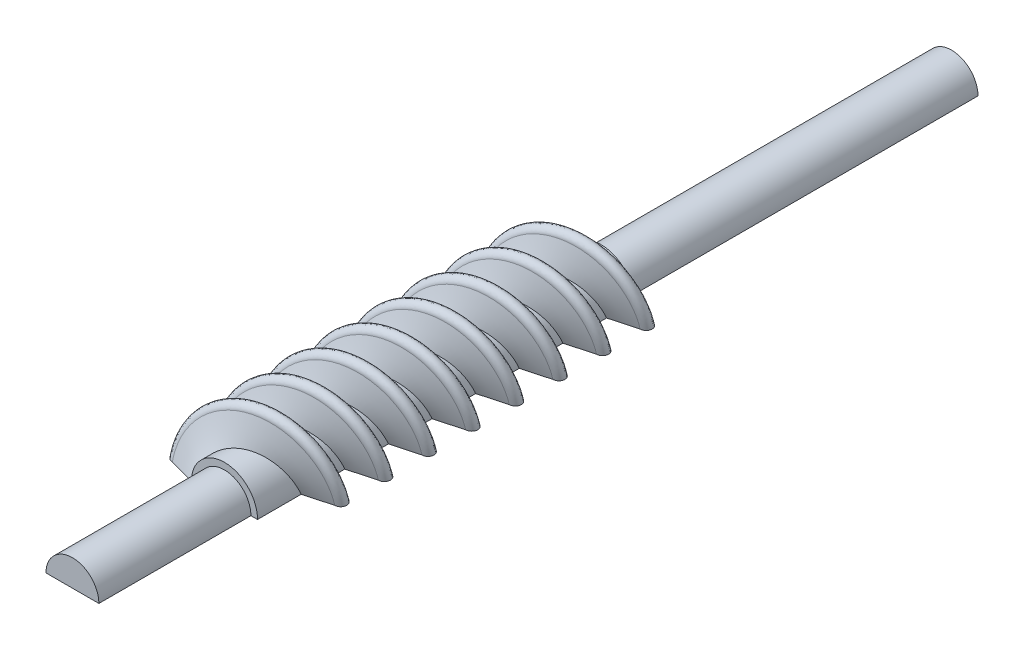
SolidWorks part; units mm, degrees
ref_plane "Plan de face" through (0, 0, 0) normal (0, 0, 1) x (1, 0, 0)
ref_plane "Plan de dessus" through (0, 0, 0) normal (0, 1, 0) x (1, 0, 0)
ref_plane "Plan de droite" through (0, 0, 0) normal (1, 0, 0) x (0, 0, -1)
sketch "Esquisse1" plane through (0, 0, 0) normal (0, 0, 1) x (1, 0, 0)
  circle A0 centre (0, 0) radius 5
  dimension "D1" = 10
extrude "Boss.-Extru.1" add sketch "Esquisse1" along normal blind 55
sketch "Esquisse3" plane through (0, 0, 55) normal (0, 0, 1) x (1, 0, 0)
  circle A0 centre (0, 0) radius 5
curve "Hélice/Spirale1" pitch 13.2 height 52.8 turns 4
sketch "Esquisse4" plane through (0, 0, 0) normal (0, 1, 0) x (1, 0, 0)
  line L0 (-5, -55) -> (-9, -55) construction
  line L1 (-5, 0) -> (-5, -55) construction
  line L2 (-9, -54.1) -> (-5, -53)
  line L3 (-9, -55.9) -> (-5, -57)
  line L5 (-5, -53) -> (-4.702, -53)
  line L6 (-4.702, -53) -> (-4.702, -57)
  line L7 (-4.702, -57) -> (-5, -57)
  arc A1 (-9, -54.1) -> (-9, -55.9) centre (-9, -55) ccw
  spline S0 degree 3 poles (-5, -55) (-5, -54.7265) (-4.7397, -54.1743) (-3.6276, -53.3502) (-1.9632, -52.525) (0, -51.7) (1.9632, -50.875) (3.6276, -50.05) (4.7397, -49.225) (5.1302, -48.4) (4.7397, -47.575) (3.6276, -46.75) (1.4084, -45.65) (-1.4084, -44.55) (-3.6276, -43.45) (-4.7397, -42.625) (-5.1302, -41.8) (-4.7397, -40.975) (-3.6276, -40.15) (-1.4084, -39.05) (1.4084, -37.95) (3.6276, -36.85) (4.7397, -36.025) (5.1302, -35.2) (4.7397, -34.375) (3.6276, -33.55) (1.4084, -32.45) (-1.4084, -31.35) (-3.6276, -30.25) (-4.7397, -29.425) (-5.1302, -28.6) (-4.7397, -27.775) (-3.6276, -26.95) (-1.4084, -25.85) (1.4084, -24.75) (3.6276, -23.65) (4.7397, -22.825) (5.1302, -22) (4.7397, -21.175) (3.6276, -20.35) (1.4084, -19.25) (-1.4084, -18.15) (-3.6276, -17.05) (-4.7397, -16.225) (-5.1302, -15.4) (-4.7397, -14.575) (-3.6276, -13.75) (-1.4084, -12.65) (1.4084, -11.55) (3.6276, -10.45) (4.7397, -9.625) (5.1302, -8.8) (4.7397, -7.975) (3.6276, -7.15) (1.9632, -6.325) (0, -5.5) (-1.9632, -4.675) (-3.6276, -3.8498) (-4.7397, -3.0257) (-5, -2.4735) (-5, -2.2) knots 0 0 0 0 0.015625 0.03125 0.046875 0.0625 0.078125 0.09375 0.109375 0.125 0.140625 0.15625 0.171875 0.203125 0.21875 0.234375 0.25 0.265625 0.28125 0.296875 0.328125 0.34375 0.359375 0.375 0.390625 0.40625 0.421875 0.453125 0.46875 0.484375 0.5 0.515625 0.53125 0.546875 0.578125 0.59375 0.609375 0.625 0.640625 0.65625 0.671875 0.703125 0.71875 0.734375 0.75 0.765625 0.78125 0.796875 0.828125 0.84375 0.859375 0.875 0.890625 0.90625 0.921875 0.9375 0.953125 0.96875 0.984375 1 1 1 1 construction
  dimension "D3" = 0.9
  dimension "D1" = 4
  dimension "D2" = 4
sweep "Balayage2" add profiles "Esquisse4" path "Hélice/Spirale1"
pattern_circular "CirPattern1" count 2 over 360 about axis through (0, 0, 55) along (0, 0, -1) of "Balayage2"
sketch "arbre" plane through (0, 0, 0) normal (0, 0, -1) x (-1, 0, 0)
  circle A0 centre (0, 0) radius 4
  dimension "D1" = 8
extrude "Motor-side" add sketch "arbre" along normal blind 53 separate body
sketch "Sketch1" plane through (0, 0, 55) normal (0, 0, 1) x (1, 0, 0)
  circle A0 centre (0, 0) radius 4
  dimension "D1" = 8
extrude "Bearing-side" add sketch "Sketch1" along normal blind 25
sketch "Sketch2" plane through (0, 0, 55) normal (0, 0, 1) x (1, 0, 0)
  circle A0 centre (0, 0) radius 5
  dimension "D1" = 10
extrude "Boss-Extrude2" add sketch "Sketch2" along normal blind 2
sketch "Sketch3" plane through (0, 0, 80) normal (0, 0, 1) x (1, 0, 0)
  line L9 (-17.0031, 0) -> (18.8779, 0)
  line L10 (-17.0031, 0) -> (-17.0031, -11.3331)
  line L11 (-17.0031, -11.3331) -> (18.8779, -11.3331)
  line L12 (18.8779, 0) -> (18.8779, -11.3331)
extrude "Cut-Extrude1" cut sketch "Sketch3" against normal through all
